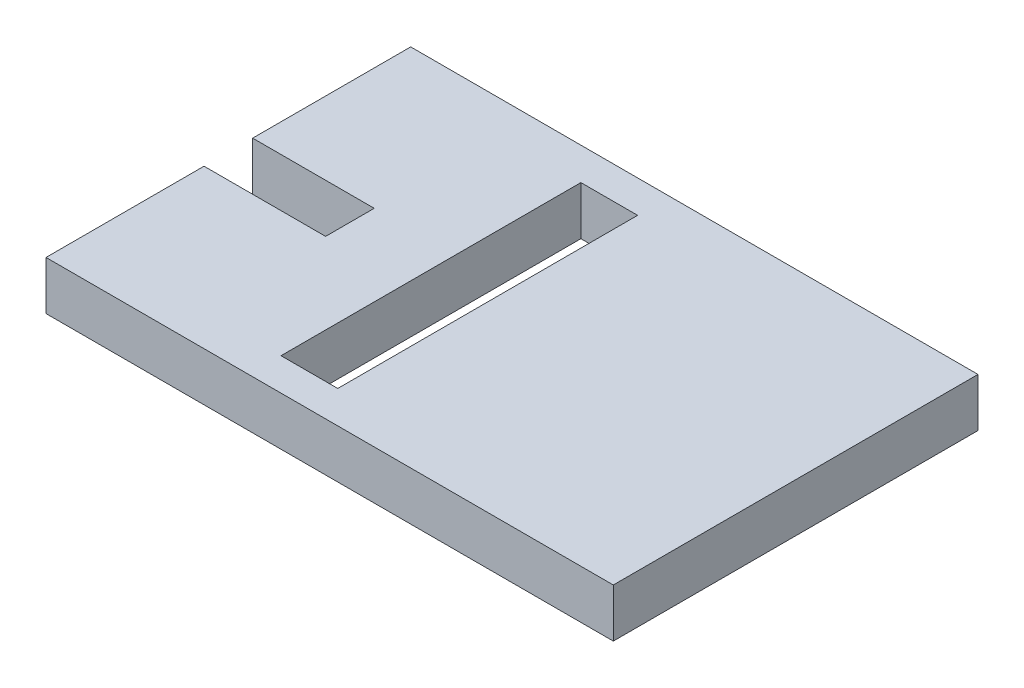
SolidWorks part; units mm, degrees
ref_plane "Спереди" through (0, 0, 0) normal (0, 0, 1) x (1, 0, 0)
ref_plane "Сверху" through (0, 0, 0) normal (0, 1, 0) x (1, 0, 0)
ref_plane "Справа" through (0, 0, 0) normal (1, 0, 0) x (0, 0, -1)
sketch "Эскиз1" plane through (0, 0, 0) normal (0, 1, 0) x (1, 0, 0)
  line L0 (-35, 3) -> (-35, 22.5)
  line L1 (-35, -22.5) -> (35, -22.5)
  line L2 (-35, -22.5) -> (-35, -3)
  line L3 (-35, 22.5) -> (35, 22.5)
  line L4 (35, -22.5) -> (35, 22.5)
  line L5 (-35, -22.5) -> (35, 22.5) construction
  line L6 (-35, 22.5) -> (35, -22.5) construction
  line L7 (-35, -3) -> (-20, -3)
  line L8 (-35, 0) -> (49965, 0) construction
  line L9 (-35, 3) -> (-20, 3)
  line L10 (-20, -3) -> (-20, 3)
  line L11 (-3, -18.5) -> (-10, -18.5)
  line L12 (-3, -18.5) -> (-3, 18.5)
  line L13 (-3, 18.5) -> (-10, 18.5)
  line L14 (-10, -18.5) -> (-10, 18.5)
  line L15 (-3, -18.5) -> (-10, 18.5) construction
  line L16 (-3, 18.5) -> (-10, -18.5) construction
  point P0 (0, 0)
  point P6 (-35, 0)
  point P8 (-6.5, 0)
  point P18 (35, 0)
  dimension "D1" = 70
  dimension "D2" = 45
  dimension "D3" = 7
  dimension "D4" = 6
  dimension "D5" = 37
  dimension "D6" = 38
  dimension "D7" = 15
extrude "Бобышка-Вытянуть1" add sketch "Эскиз1" along normal blind 6
